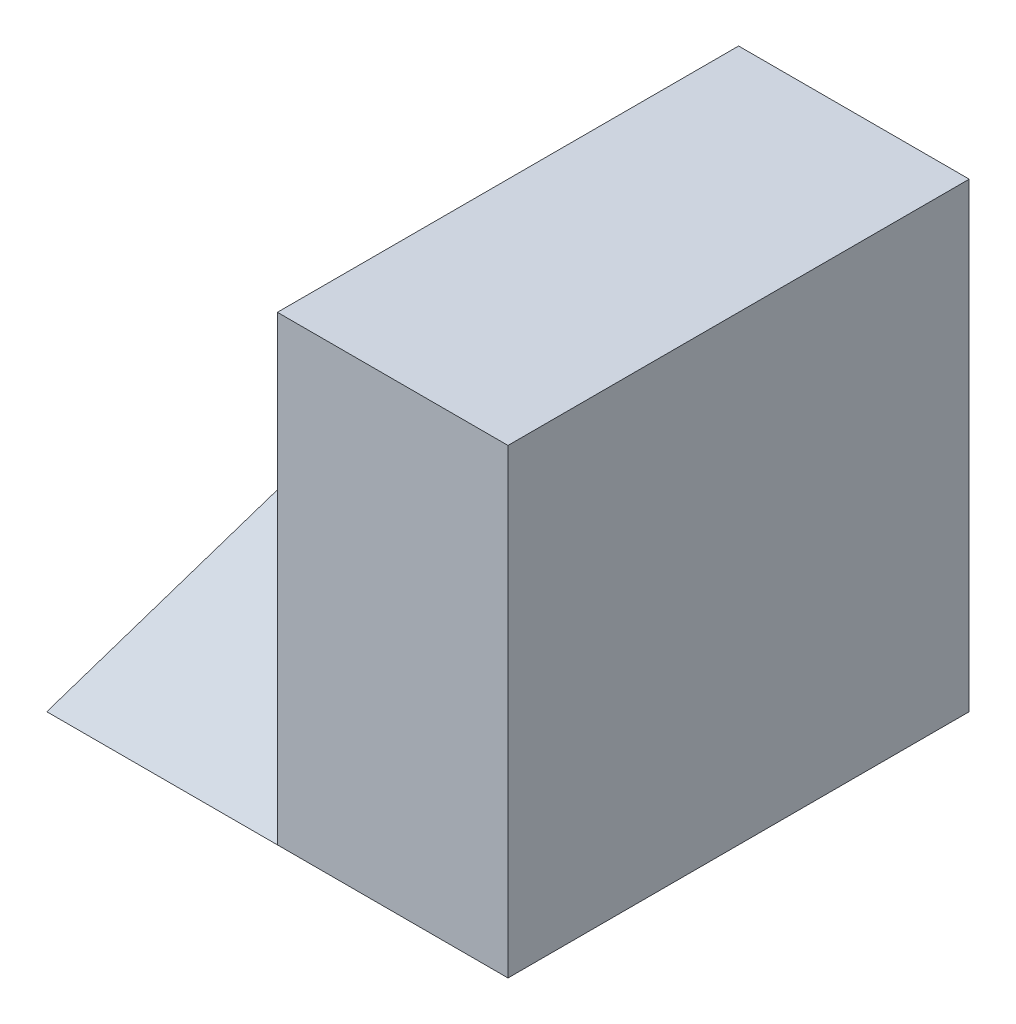
SolidWorks part; units mm, degrees
ref_plane "Front Plane" through (0, 0, 0) normal (0, 0, 1) x (1, 0, 0)
ref_plane "Top Plane" through (0, 0, 0) normal (0, 1, 0) x (1, 0, 0)
ref_plane "Right Plane" through (0, 0, 0) normal (1, 0, 0) x (0, 0, -1)
sketch "Sketch1" plane through (0, 0, 0) normal (0, 0, 1) x (1, 0, 0)
  line L1 (0, 0) -> (40, 0)
  line L2 (0, 0) -> (0, 40)
  line L3 (0, 40) -> (40, 40)
  line L4 (40, 0) -> (40, 40)
  dimension "D1" = 40
  dimension "D2" = 40
extrude "Boss-Extrude1" add sketch "Sketch1" along normal blind 40
sketch "Sketch2" plane through (0, 0, 40) normal (0, 0, 1) x (1, 0, 0)
  line L0 (0, 0) -> (20, 40)
  line L1 (40, 40) -> (0, 40) construction
  line L2 (20, 40) -> (0, 40)
  line L3 (0, 40) -> (0, 0)
extrude "Cut-Extrude1" cut sketch "Sketch2" against normal blind 40
ref_plane "Plane1" through (16, 0, 8) normal (0.8944, 0, 0.4472) x (0.4472, 0, -0.8944)
ref_plane "Plane2" through (0, 0, 0) normal (0.6667, -0.6667, 0.3333) x (-0.7454, -0.5963, 0.2981)
ref_plane "Plane3" through (16, 0, 8) normal (0.8944, 0, 0.4472) x (0.4472, 0, -0.8944)
sketch "Sketch7" plane through (0, 0, 40) normal (0, 0, 1) x (1, 0, 0)
  line L0 (20, 40) -> (20, 0)
  line L1 (0, 0) -> (40, 0) construction
  line L2 (20, 0) -> (0, 0)
  line L3 (0, 0) -> (20, 40)
extrude "Cut-Extrude4" cut sketch "Sketch7" against normal blind 20
sketch "Sketch8" plane through (0, 0, 20) normal (0, 0, 1) x (1, 0, 0)
  line L0 (20, 40) -> (0, 0)
  line L1 (0, 0) -> (20, 0)
  line L2 (20, 0) -> (20, 40)
extrude "Cut-Extrude5" cut sketch "Sketch8" against normal blind 20
sketch "Sketch9" plane through (20, 0, 0) normal (-1, 0, 0) x (0, 0, 1)
  line L0 (0, 40) -> (40, 0)
  line L1 (40, 0) -> (0, 0)
  line L2 (0, 0) -> (0, 40)
extrude "Boss-Extrude2" add sketch "Sketch9" along normal blind 20
sketch "Sketch10" plane through (0, 0, 0) normal (0, 0, -1) x (-1, 0, 0)
  line L0 (0, 0) -> (-20, 40)
  line L1 (-20, 40) -> (0, 40)
  line L2 (0, 40) -> (0, 0)
extrude "Cut-Extrude6" cut sketch "Sketch10" against normal blind 50
